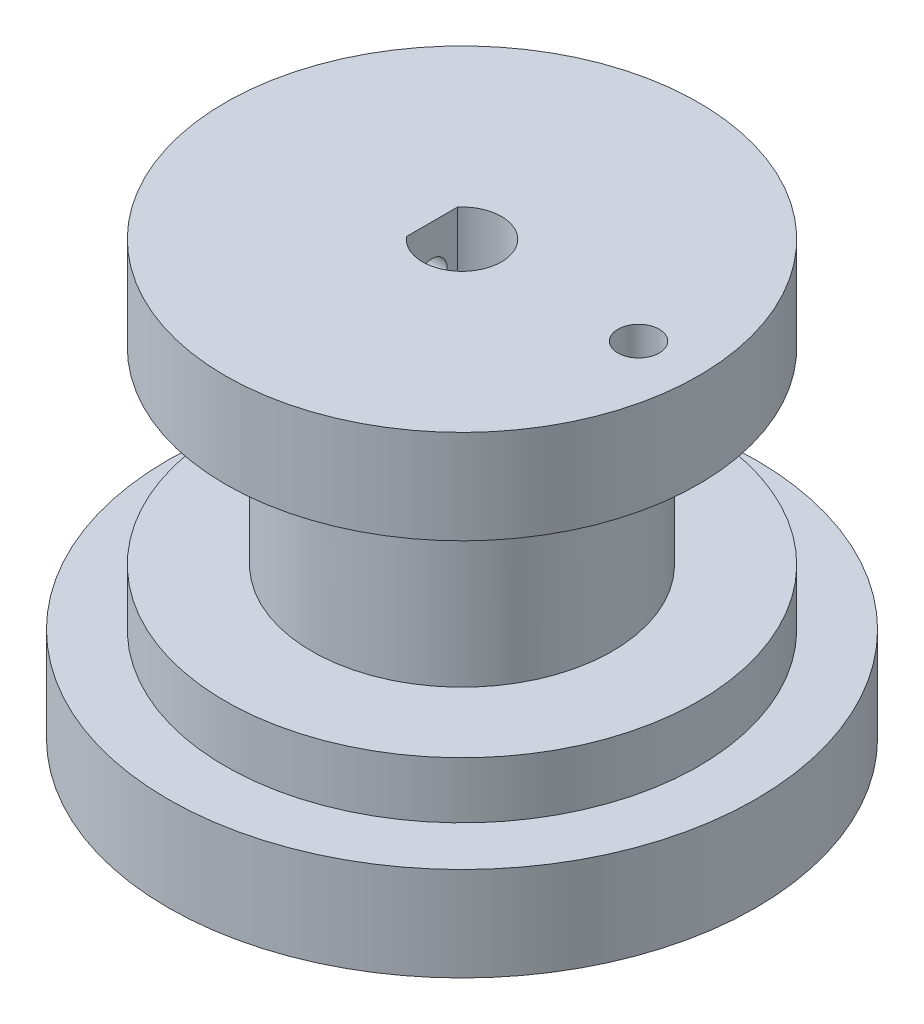
SolidWorks part; units mm, degrees
ref_plane "Front Plane" through (0, 0, 0) normal (0, 0, 1) x (1, 0, 0)
ref_plane "Top Plane" through (0, 0, 0) normal (0, 1, 0) x (1, 0, 0)
ref_plane "Right Plane" through (0, 0, 0) normal (1, 0, 0) x (0, 0, -1)
sketch "Sketch1" plane through (0, 0, 0) normal (0, 1, 0) x (1, 0, 0)
  circle A0 centre (0, 0) radius 8
extrude "Boss-Extrude1" add sketch "Sketch1" along normal blind 10 contours A0
sketch "Sketch2" plane through (0, 0, 0) normal (0, -1, 0) x (1, 0, 0)
  circle A0 centre (0, 0) radius 12.6
sketch "Sketch3" plane through (0, 10, 0) normal (0, 1, 0) x (1, 0, 0)
  circle A0 centre (0, 0) radius 12.6
extrude "Boss-Extrude2" add sketch "Sketch2" along normal blind 3 contours A0
sketch "Sketch4" plane through (0, 10, 0) normal (0, 1, 0) x (1, 0, 0)
  circle A0 centre (0, 0) radius 1.5
extrude "Cut-Extrude4" cut sketch "Sketch4" against normal up to surface (13 mm away) contours A0 up to face at (0, -3, -12.6)
extrude "Boss-Extrude4" add sketch "Sketch3" along normal blind 5 contours A0
sketch "Sketch5" plane through (0, 15, 0) normal (0, 1, 0) x (1, 0, 0)
  circle A0 centre (0, 0) radius 2.1
extrude "Cut-Extrude5" cut sketch "Sketch5" against normal through all contours A0
sketch "Sketch6" plane through (0, 15, 0) normal (0, 1, 0) x (1, 0, 0)
  line L1 (-2.6, 2.4469) -> (-1.6, 2.4469)
  line L2 (-2.6, 2.4469) -> (-2.6, -2.4469)
  line L3 (-2.6, -2.4469) -> (-1.6, -2.4469)
  line L4 (-1.6, 2.4469) -> (-1.6, -2.4469)
  line L5 (-2.6, 2.4469) -> (-1.6, -2.4469) construction
  line L6 (-2.6, -2.4469) -> (-1.6, 2.4469) construction
  point P0 (-2.1, 0)
  dimension "D1" = 2.1
  dimension "D2" = 1
extrude "Boss-Extrude5" add sketch "Sketch6" against normal blind 8 contours L4 L3 L2 L1
ref_plane "Plane1" through (-12.6, 0, 0) normal (-1, 0, 0) x (0, 0, 1)
hole_wizard "Tap Drill for M2x0.4 Tap1" positions "Sketch15" profile "Sketch14" hole size "M2x0.4" standard "ANSI Metric"
sketch "Sketch15" plane through (-12.6, 0, 0) normal (-1, 0, 0) x (0, 0, 1)
  line L0 (12.6, 15) -> (-12.6, 15) construction
  point P0 (0, 12.5)
  point P2 (0, 12.5)
  dimension "D1" = 2.5
sketch "Sketch14" plane through (-12.6, 12.5, 0) normal (0, 1, 0) x (0, 0, 1)
  line L0 (0, 0) -> (0, 16.4807)
  line L1 (0, 16.4807) -> (0.8, 16)
  line L2 (0.8, 16) -> (0.8, 0)
  line L5 (0.8, 0) -> (0, 0)
  line L10 (0, 16.4807) -> (-0.8, 16) construction
  line L11 (0, -6.35) -> (0, 107.95) construction
  dimension "Hole Dia." = 1.6
  dimension "Hole Depth" = 16
  dimension "Drill Angle" = 118
sketch "Sketch16" plane through (0, -3, 0) normal (0, -1, 0) x (-1, 0, 0)
  circle A0 centre (0, 0) radius 15.644
extrude "Boss-Extrude6" add sketch "Sketch16" along normal blind 5
sketch "Sketch17" plane through (0, -8, 0) normal (0, -1, 0) x (-1, 0, 0)
  circle A0 centre (0, 0) radius 2.1
extrude "Cut-Extrude6" cut sketch "Sketch17" against normal blind 5
sketch "Sketch18" plane through (0, 0, 0) normal (0, 1, 0) x (1, 0, 0)
  circle A0 centre (-9.4, 0) radius 1.1
  circle A1 centre (0, 0) radius 12.6 construction
  dimension "D1" = 9.4
sketch "Sketch19" plane through (0, 10, 0) normal (0, -1, 0) x (-1, 0, 0)
  circle A0 centre (-9.4, 0) radius 1.1
  circle A1 centre (0, 0) radius 8 construction
  dimension "D1" = 9.4
extrude "Cut-Extrude9" cut sketch "Sketch18" against normal through all contours A0
extrude "Cut-Extrude10" cut sketch "Sketch19" against normal blind 10 contours A0
sketch "Sketch21" plane through (0, 10, 0) normal (0, 1, 0) x (1, 0, 0)
  circle A0 centre (0, 0) radius 2.1
sketch "Sketch22" plane through (0, 10, 0) normal (0, 1, 0) x (-1, 0, 0)
  line L1 (2.6, -1.5397) -> (1.6, -1.5397)
  line L2 (2.6, -1.5397) -> (2.6, 1.5397)
  line L3 (2.6, 1.5397) -> (1.6, 1.5397)
  line L4 (1.6, -1.5397) -> (1.6, 1.5397)
  line L5 (2.6, -1.5397) -> (1.6, 1.5397) construction
  line L6 (2.6, 1.5397) -> (1.6, -1.5397) construction
  point P0 (2.1, 0)
  dimension "D1" = 1
  dimension "D2" = 2.1
extrude "Cut-Extrude11" [suppressed] cut sketch "Sketch21" against normal through all contours A0
extrude "Boss-Extrude8" [suppressed] add sketch "Sketch22" against normal blind 42 contours L3 L4 L1 L2
